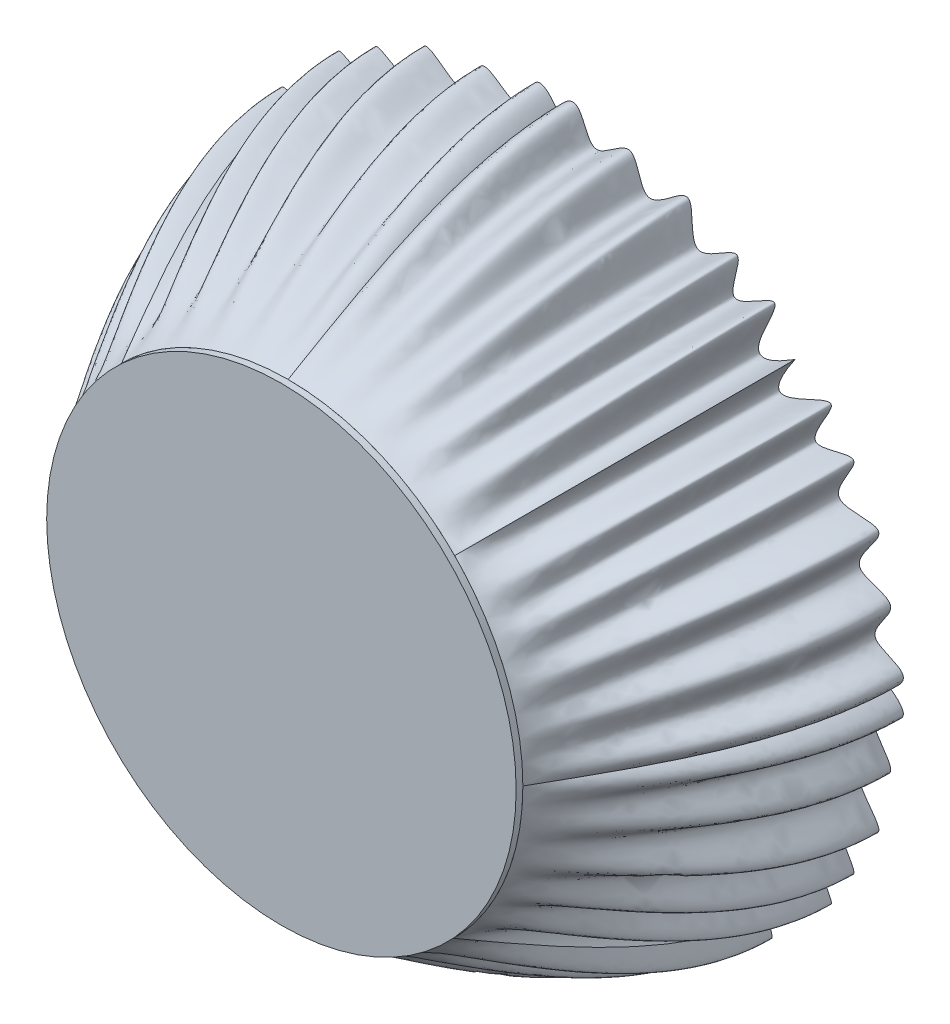
SolidWorks part; units mm, degrees
ref_plane "Front Plane" through (0, 0, 0) normal (0, 0, 1) x (1, 0, 0)
ref_plane "Top Plane" through (0, 0, 0) normal (0, 1, 0) x (1, 0, 0)
ref_plane "Right Plane" through (0, 0, 0) normal (1, 0, 0) x (0, 0, -1)
sketch "Sketch1" plane through (0, 0, 0) normal (0, 0, 1) x (1, 0, 0)
  spline S0 degree 3 poles (0, 100) (7.9771, 111.0107) (7.3539, 86.0534) (24.0638, 106.7427) (25.1348, 83.0233) (43.2294, 105.326) (37.7107, 76.5148) (59.3271, 96.7585) (47.3961, 70.2416) (78.5384, 95.2355) (48.8759, 56.7698) (71.1492, 70.7107) knots 0 0 0 0 0.129605 0.221662 0.306505 0.413963 0.511893 0.612904 0.702981 0.804918 1 1 1 1
  spline S1 degree 3 poles (99.5614, 0) (110.1021, 7.5751) (85.749, 7.0781) (106.3228, 23.6289) (82.5784, 24.695) (104.8893, 42.7911) (76.075, 37.2724) (96.3228, 58.8872) (69.7935, 46.9621) (94.9151, 78.1482) (55.8445, 48.3652) (71.1492, 70.7107) knots 0 0 0 0 0.126596 0.21887 0.303914 0.411627 0.509789 0.611039 0.701329 0.803508 1 1 1 1
  spline S2 degree 3 poles (99.5614, 0) (110.1021, -7.5751) (85.749, -7.0781) (106.3228, -23.6289) (82.5784, -24.695) (104.8891, -42.7912) (76.0758, -37.272) (96.32, -58.8885) (69.803, -46.9575) (94.797, -78.0998) (56.3312, -48.4373) (70.2721, -70.7107) knots 0 0 0 0 0.126716 0.219078 0.304203 0.412018 0.510273 0.611619 0.701995 0.804271 1 1 1 1
  spline S3 degree 3 poles (0, -100) (7.173, -110.0945) (6.8018, -86.315) (23.1939, -106.7815) (24.2552, -83.0102) (42.3529, -105.3295) (36.8334, -76.5138) (58.45, -96.7587) (46.5189, -70.2415) (77.6613, -95.2356) (47.9987, -56.7698) (70.2721, -70.7107) knots 0 0 0 0 0.123834 0.216501 0.301907 0.410078 0.508657 0.610338 0.701011 0.803625 1 1 1 1
  spline S4 degree 3 poles (0, -100) (-7.173, -110.0945) (-6.8018, -86.315) (-23.1939, -106.7815) (-24.2552, -83.0102) (-42.3529, -105.3295) (-36.8334, -76.5138) (-58.45, -96.7587) (-46.5189, -70.2415) (-77.6613, -95.2356) (-47.9987, -56.7698) (-70.2721, -70.7107) knots 0 0 0 0 0.123834 0.216501 0.301907 0.410078 0.508657 0.610338 0.701011 0.803625 1 1 1 1
  spline S5 degree 3 poles (-99.5614, 0) (-110.1021, -7.5751) (-85.749, -7.0781) (-106.3228, -23.6289) (-82.5784, -24.695) (-104.8891, -42.7912) (-76.0758, -37.272) (-96.32, -58.8885) (-69.803, -46.9575) (-94.797, -78.0998) (-56.3312, -48.4373) (-70.2721, -70.7107) knots 0 0 0 0 0.126716 0.219078 0.304203 0.412018 0.510273 0.611619 0.701995 0.804271 1 1 1 1
  spline S6 degree 3 poles (-99.5614, 0) (-110.1021, 7.5751) (-85.749, 7.0781) (-106.3228, 23.6289) (-82.5784, 24.695) (-104.8893, 42.7911) (-76.075, 37.2724) (-96.3228, 58.8872) (-69.7935, 46.9621) (-94.9151, 78.1482) (-55.8445, 48.3652) (-71.1492, 70.7107) knots 0 0 0 0 0.126596 0.21887 0.303914 0.411627 0.509789 0.611039 0.701329 0.803508 1 1 1 1
  spline S7 degree 3 poles (0, 100) (-7.9771, 111.0107) (-7.3539, 86.0534) (-24.0638, 106.7427) (-25.1348, 83.0233) (-43.2294, 105.326) (-37.7107, 76.5148) (-59.3271, 96.7585) (-47.3961, 70.2416) (-78.5384, 95.2355) (-48.8759, 56.7698) (-71.1492, 70.7107) knots 0 0 0 0 0.129605 0.221662 0.306505 0.413963 0.511893 0.612904 0.702981 0.804918 1 1 1 1
ref_plane "Plane1" through (0, 0, 80) normal (0, 0, 1) x (1, 0, 0)
sketch "Sketch2" plane through (0, 0, 80) normal (0, 0, 1) x (1, 0, 0)
  circle A0 centre (0, 0) radius 70
surface "Surface-Loft1"
sketch "Sketch3" plane through (0, 0, 80) normal (0, 0, 1) x (1, 0, 0)
  circle A0 centre (0, 0) radius 70
extrude "Boss-Extrude1" add sketch "Sketch3" along normal blind 2
